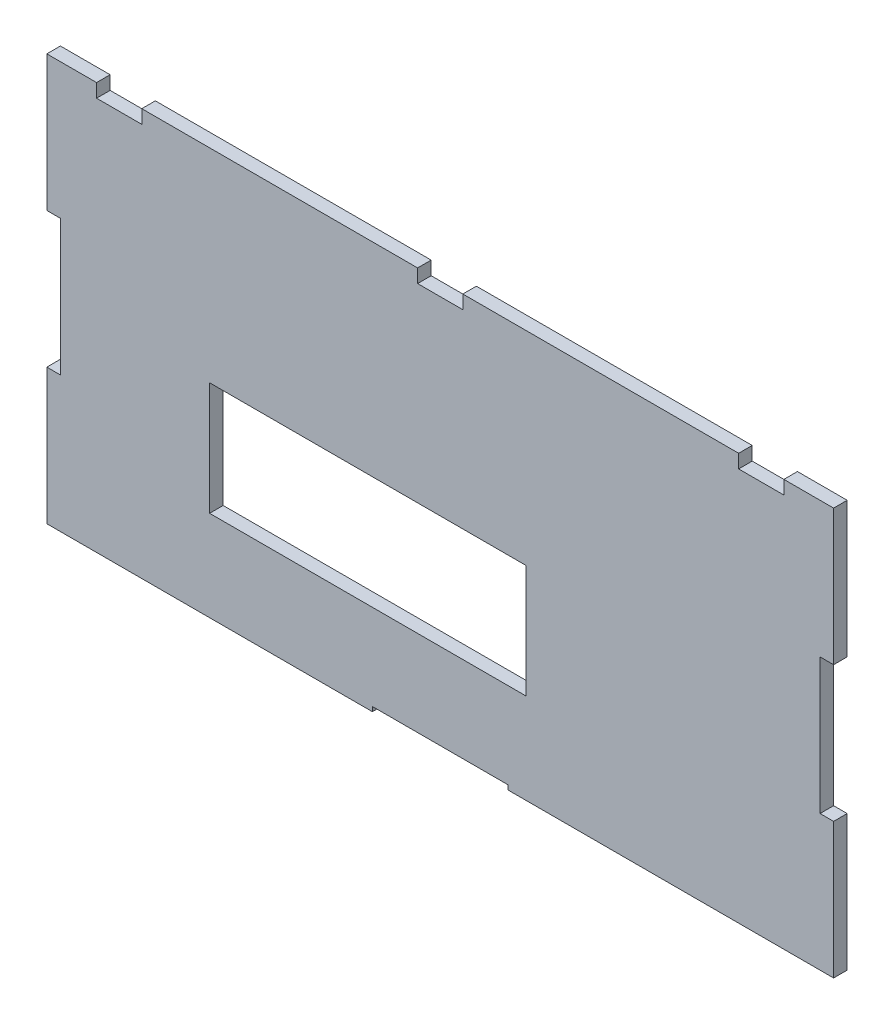
SolidWorks part; units mm, degrees
ref_plane "Front Plane" through (0, 0, 0) normal (0, 0, 1) x (1, 0, 0)
ref_plane "Top Plane" through (0, 0, 0) normal (0, 1, 0) x (1, 0, 0)
ref_plane "Right Plane" through (0, 0, 0) normal (1, 0, 0) x (0, 0, -1)
sketch "Model" plane through (0, 0, 0) normal (0, 0, 1) x (1, 0, 0)
  line L0 (249.4029, 1.9153) -> (249.4029, -28.0847)
  line L1 (180.4029, -58.0847) -> (180.4029, -57.0847)
  line L2 (180.4029, -57.0847) -> (150.4029, -57.0847)
  line L3 (150.4029, -57.0847) -> (150.4029, -58.0847)
  line L4 (180.4029, -58.0847) -> (252.4029, -58.0847)
  line L5 (115.4029, 31.9153) -> (235.4029, 31.9153) construction
  line L6 (78.4029, 31.9153) -> (89.4029, 31.9153)
  line L7 (89.4029, 31.9153) -> (89.4029, 28.9153)
  line L8 (89.4029, 28.9153) -> (99.4029, 28.9153)
  line L9 (99.4029, 28.9153) -> (99.4029, 31.9153)
  line L10 (99.4029, 31.9153) -> (160.4029, 31.9153)
  line L11 (160.4029, 31.9153) -> (160.4029, 28.9153)
  line L12 (160.4029, 28.9153) -> (170.4029, 28.9153)
  line L13 (170.4029, 28.9153) -> (170.4029, 31.9153)
  line L14 (170.4029, 31.9153) -> (231.4029, 31.9153)
  line L15 (231.4029, 31.9153) -> (231.4029, 28.9153)
  line L16 (231.4029, 28.9153) -> (241.4029, 28.9153)
  line L17 (241.4029, 28.9153) -> (241.4029, 31.9153)
  line L18 (241.4029, 31.9153) -> (252.4029, 31.9153)
  line L376 (184.4029, -38.0847) -> (114.4029, -38.0847)
  line L377 (114.4029, -38.0847) -> (114.4029, -13.0847)
  line L378 (114.4029, -13.0847) -> (184.4029, -13.0847)
  line L379 (184.4029, -13.0847) -> (184.4029, -38.0847)
  line L380 (252.4029, -28.0847) -> (249.4029, -28.0847)
  line L398 (249.4029, 1.9153) -> (252.4029, 1.9153)
  line L399 (252.4029, 1.9153) -> (252.4029, 31.9153)
  line L400 (252.4029, 31.9153) -> (235.4029, 31.9153) construction
  line L440 (115.4029, 31.9153) -> (78.4029, 31.9153) construction
  line L441 (78.4029, 31.9153) -> (78.4029, 1.9153)
  line L442 (78.4029, 1.9153) -> (81.4029, 1.9153)
  line L443 (81.4029, 1.9153) -> (81.4029, -28.0847)
  line L460 (81.4029, -28.0847) -> (78.4029, -28.0847)
  line L461 (78.4029, -28.0847) -> (78.4029, -58.0847)
  line L462 (78.4029, -58.0847) -> (150.4029, -58.0847)
  line L463 (252.4029, -58.0847) -> (252.4029, -28.0847)
  dimension "D1" = 30
  dimension "D2" = 30
  dimension "D3" = 30
  dimension "D4" = 30
  dimension "D5" = 30
  dimension "D6" = 30
  dimension "D7" = 11
  dimension "D8" = 10
  dimension "D9" = 11
  dimension "D10" = 3
  dimension "D11" = 3
  dimension "D12" = 1
  dimension "D13" = 30
  dimension "D14" = 72
  dimension "D15" = 70
  dimension "D16" = 70
  dimension "D17" = 25
  dimension "D18" = 10
  dimension "D19" = 65
  dimension "D20" = 3
  dimension "D21" = 3
  dimension "D22" = 3
  dimension "D23" = 10
  dimension "D24" = 82
  dimension "D25" = 174
extrude "Boss-Extrude1" add sketch "Model" along normal blind 3
